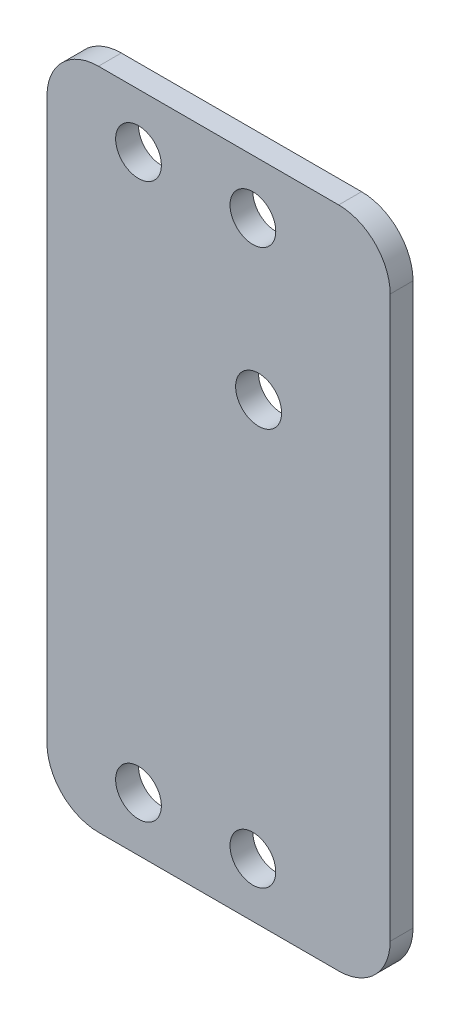
SolidWorks part; units mm, degrees
ref_plane "Front Plane" through (0, 0, 0) normal (0, 0, 1) x (1, 0, 0)
ref_plane "Top Plane" through (0, 0, 0) normal (0, 1, 0) x (1, 0, 0)
ref_plane "Right Plane" through (0, 0, 0) normal (1, 0, 0) x (0, 0, -1)
sketch "Sketch1" plane through (0, 0, 0) normal (0, 0, 1) x (1, 0, 0)
  line L1 (-15, 29) -> (15, 29)
  line L2 (-15, 29) -> (-15, -29)
  line L3 (-15, -29) -> (15, -29)
  line L4 (15, 29) -> (15, -29)
  circle A0 centre (3, 24.25) radius 2
  circle A1 centre (-7, 24.25) radius 2
  circle A2 centre (-7, -24.25) radius 2
  circle A3 centre (3, -24.25) radius 2
  circle A4 centre (3.5, 10.75) radius 2.01
  point P4 (0, 29)
  point P6 (-15, 0)
  dimension "D3" = 4.02
  dimension "D1" = 58
  dimension "D2" = 30
extrude "Boss-Extrude1" add sketch "Sketch1" along normal blind 2
fillet "Fillet1" radius 4.5 4 edges at (15, -29, 1) (-15, -29, 1) (15, 29, 1) (-15, 29, 1)
